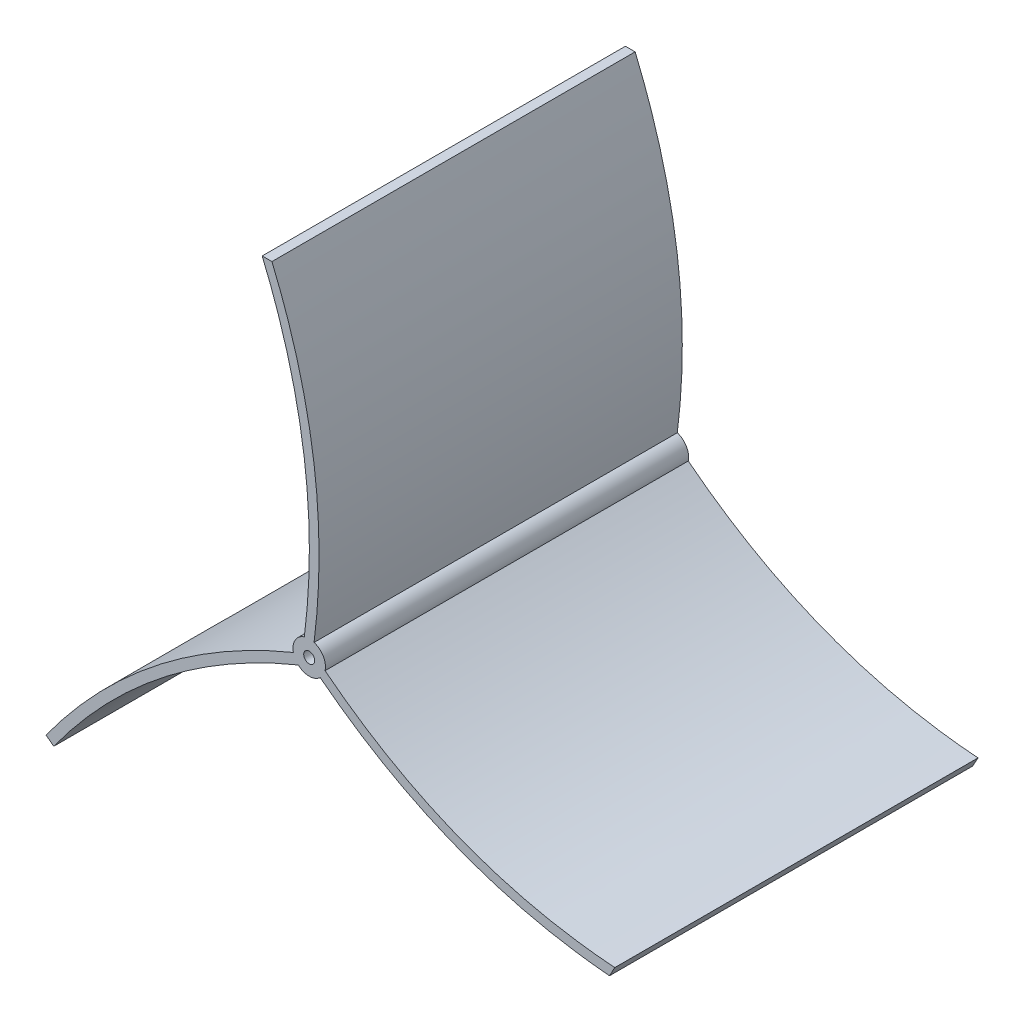
SolidWorks part; units mm, degrees
material "尼龙 101"
ref_plane "前视基准面" through (0, 0, 0) normal (0, 0, 1) x (1, 0, 0)
ref_plane "上视基准面" through (0, 0, 0) normal (0, 1, 0) x (1, 0, 0)
ref_plane "右视基准面" through (0, 0, 0) normal (1, 0, 0) x (0, 0, -1)
other "Configuration Table"
sketch "草图1" plane through (0, 0, 0) normal (0, 0, 1) x (1, 0, 0)
  line L0 (0.2591, 0.9775) -> (0.2591, 100.9775) construction
  line L1 (0.2591, 0.9775) -> (-86.3434, -49.0225) construction
  line L2 (0.2591, 0.9775) -> (86.8617, -49.0225) construction
  line L3 (-4.6215, -0.1083) -> (-87.0837, -47.7178) construction
  line L4 (3.6398, -2.7064) -> (86.1019, -50.3159) construction
  line L5 (1.7591, 5.7472) -> (1.7591, 100.9662) construction
  line L6 (-3.1215, -2.7064) -> (-85.5837, -50.3159) construction
  line L7 (5.1398, -0.1083) -> (87.6019, -47.7178) construction
  line L8 (-1.2409, 5.7472) -> (-1.2409, 100.9662) construction
  line L9 (1.0091, 2.2765) -> (87.6117, -47.7235) construction
  line L10 (-0.4909, -0.3215) -> (86.1117, -50.3215) construction
  line L11 (-0.4909, 2.2765) -> (-87.0934, -47.7235) construction
  line L12 (1.0091, -0.3215) -> (-85.5934, -50.3215) construction
  line L13 (-1.2409, 0.9775) -> (-1.2409, 100.9775) construction
  line L14 (1.7591, 0.9775) -> (1.7591, 100.9775) construction
  line L15 (-14.2409, 100.9662) -> (-11.2409, 100.9662)
  line L16 (-78.5012, -62.1112) -> (-80.9047, -60.3159)
  line L17 (92.8499, -37.7178) -> (94.4819, -34.7178)
  arc A0 (-87.0837, -47.7178) -> (-85.5837, -50.3159) centre (0.2591, 0.9775) ccw construction
  circle A1 centre (0.2591, 0.9775) radius 1.7
  arc A2 (-1.2409, 5.7472) -> (-4.6215, -0.1083) centre (0.2591, 0.9775) ccw construction
  arc A3 (86.1019, -50.3159) -> (87.6019, -47.7178) centre (0.2591, 0.9775) ccw construction
  arc A4 (1.7591, 100.9662) -> (-1.2409, 100.9662) centre (0.2591, 0.9775) ccw construction
  arc A5 (-3.1215, -2.7064) -> (3.6398, -2.7064) centre (0.2591, 0.9775) ccw construction
  arc A6 (5.1398, -0.1083) -> (1.7591, 5.7472) centre (0.2591, 0.9775) ccw construction
  arc A7 (-1.2409, 5.7472) -> (-4.6215, -0.1083) centre (0.2591, 0.9775) ccw
  arc A8 (-3.1215, -2.7064) -> (3.6398, -2.7064) centre (0.2591, 0.9775) ccw
  arc A9 (5.1398, -0.1083) -> (1.7591, 5.7472) centre (0.2591, 0.9775) ccw
  spline S0 degree 1 poles (-4.6215, -0.1083) (-87.0837, -47.7178) knots 0 0 1 1 construction
  spline S1 degree 1 poles (-4.6215, -0.1083) (-47.2639, -24.7279) knots 0 0 1 1 construction
  spline S2 degree 2 poles (1.7591, 5.7472) (8.0296, 55.0689) (-11.2409, 100.9662) knots 0 0 0 1 1 1
  spline S3 degree 2 poles (-1.2409, 5.7472) (5.0296, 55.0689) (-14.2409, 100.9662) knots 0 0 0 1 1 1
  spline S4 degree 2 poles (-4.6215, -0.1083) (-51.2237, -19.3993) (-80.9047, -60.3159) knots 0 0 0 1 1 1
  spline S5 degree 2 poles (-3.1215, -2.7064) (-49.2347, -21.6647) (-78.5012, -62.1112) knots 0 0 0 1 1 1
  spline S6 degree 2 poles (3.6398, -2.7064) (43.0248, -33.4143) (92.8499, -37.7178) knots 0 0 0 1 1 1
  spline S7 degree 2 poles (5.1398, -0.1083) (44.4962, -31.0243) (94.4819, -34.7178) knots 0 0 0 1 1 1
  dimension "D1" = 200
  dimension "D2" = 3.4
  dimension "D3" = 10
  dimension "D4" = 120
  dimension "D5" = 120
  dimension "D8" = 10
  dimension "D9" = 3
  dimension "D10" = 10
  dimension "D11" = 3
  dimension "D12" = 3
  dimension "D13" = 10
  dimension "D6" = 1.5
  dimension "D7" = 1.5
extrude "凸台-拉伸1" add sketch "草图1" along normal blind 112 contours L7 A6 L5 A4 L8 A2 L3 S0 A0 L6 A5 L4 A3 A1
